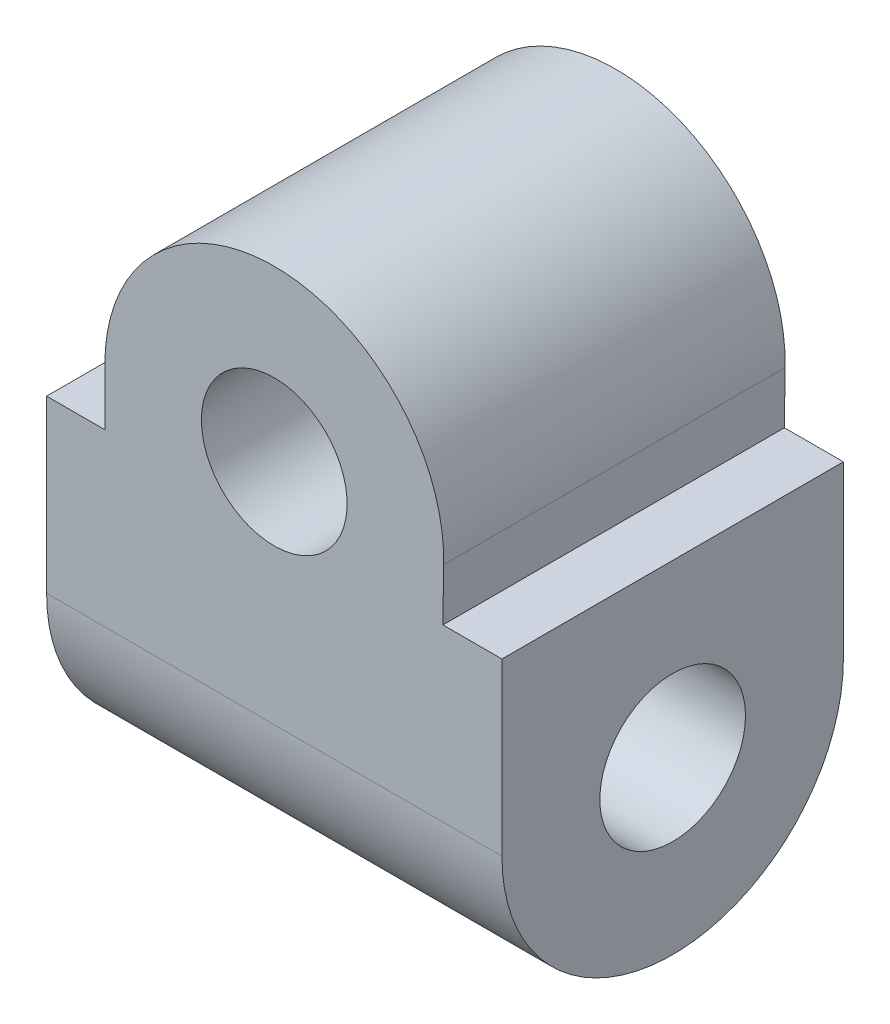
SolidWorks part; units mm, degrees
ref_plane "Front Plane" through (0, 0, 0) normal (0, 0, 1) x (1, 0, 0)
ref_plane "Top Plane" through (0, 0, 0) normal (0, 1, 0) x (1, 0, 0)
ref_plane "Right Plane" through (0, 0, 0) normal (1, 0, 0) x (0, 0, -1)
sketch "Sketch1" plane through (0, 0, 0) normal (1, 0, 0) x (0, 0, -1)
  line L0 (0, 0) -> (0, 40.9689) construction
  line L1 (15, 0) -> (15, 35)
  line L2 (-15, 0) -> (-15, 35)
  line L3 (-15, 35) -> (15, 35)
  circle A0 centre (0, 0) radius 6.4
  arc A1 (-15, 0) -> (15, 0) centre (0, 0) ccw
  dimension "D1" = 12.8
  dimension "D2" = 30
  dimension "D3" = 35
extrude "Boss-Extrude1" add sketch "Sketch1" along normal blind 40
sketch "Sketch3" plane through (0, 0, -15) normal (0, 0, -1) x (-1, 0, 0)
  line L1 (0, 0) -> (-40, 0) construction
  line L2 (-20, 0) -> (-20, 40.154) construction
  line L3 (-46.0075, 15) -> (-34.817, 15)
  line L4 (-34.817, 15) -> (-34.8773, 19.6109)
  line L5 (-5.1177, 20) -> (-5.1177, 15)
  line L6 (-46.0075, 15) -> (-46.0075, 43.038)
  line L7 (-46.0075, 43.038) -> (8.5552, 43.038)
  line L8 (8.5552, 43.038) -> (8.5552, 15)
  line L9 (-5.1177, 15) -> (8.5552, 15)
  circle A0 centre (-20, 20) radius 6.4
  arc A1 (-5.1177, 20) -> (-34.8773, 19.6109) centre (-20, 20) ccw
  dimension "D1" = 12.8
  dimension "D2" = 15
extrude "Cut-Extrude1" cut sketch "Sketch3" against normal blind 43
